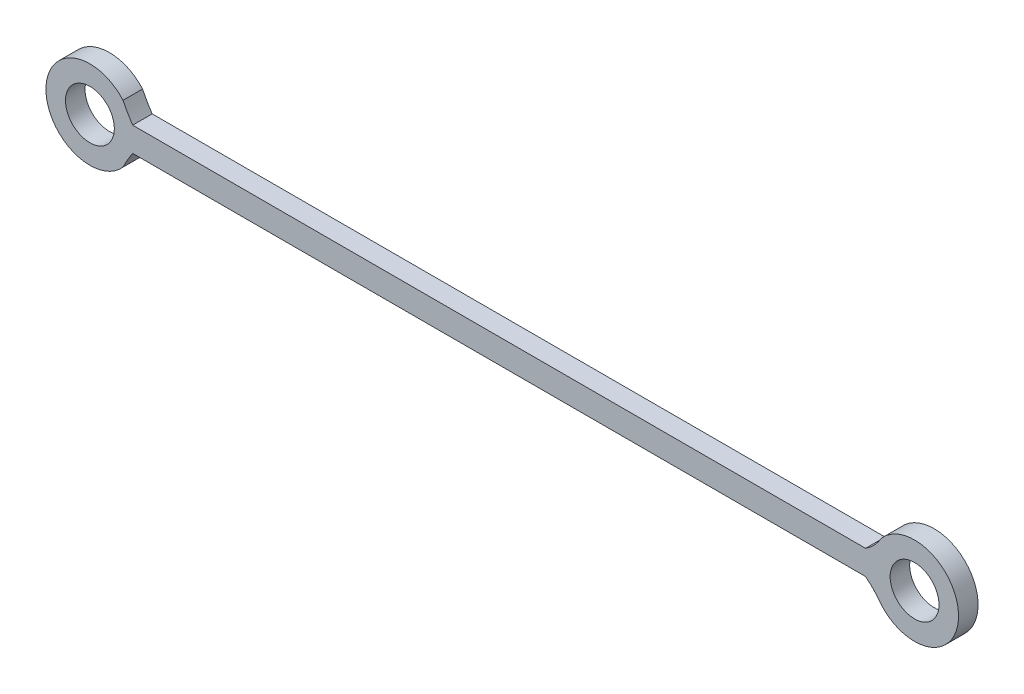
SolidWorks part; units mm, degrees
ref_plane "前视基准面" through (0, 0, 0) normal (0, 0, 1) x (1, 0, 0)
ref_plane "上视基准面" through (0, 0, 0) normal (0, 1, 0) x (1, 0, 0)
ref_plane "右视基准面" through (0, 0, 0) normal (1, 0, 0) x (0, 0, -1)
sketch "草图1" plane through (0, 0, 0) normal (0, 0, 1) x (1, 0, 0)
  line L0 (-67.4973, -2.5) -> (82.4769, -2.5)
  line L1 (82.4769, 2.5) -> (-67.4973, 2.5)
  line L2 (-124.0379, 0) -> (138.7459, 0) construction
  line L3 (-67.4973, 65.4474) -> (-67.4973, -82.036) construction
  line L4 (0, 70.9224) -> (0, -92.6625) construction
  line L5 (82.4769, 70.9224) -> (82.4769, -95.5597) construction
  circle A0 centre (92.5, 0) radius 5
  circle A1 centre (-76.25, 0) radius 5
  arc A2 (85.722, -5.9211) -> (82.4769, -2.5) centre (72.3573, -15.3486) ccw
  arc A3 (85.722, -5.9211) -> (85.722, 5.9211) centre (92.5, 0) ccw
  arc A4 (82.4769, 2.5) -> (85.722, 5.9211) centre (77.0488, 10.8985) ccw
  arc A5 (-69.472, 5.9211) -> (-67.4973, 2.5) centre (-43.5863, 18.5825) ccw
  arc A6 (-69.472, 5.9211) -> (-69.472, -5.9211) centre (-76.25, 0) ccw
  arc A7 (-67.4973, -2.5) -> (-69.472, -5.9211) centre (-43.5863, -18.5825) ccw
  dimension "D2" = 10
  dimension "D3" = 2.5
  dimension "D1" = 67.4973
  dimension "D6" = 10
  dimension "D5" = 9
  dimension "D9" = 10
  dimension "D4" = 2.5
  dimension "D8" = 168.75
extrude "凸台-拉伸1" add sketch "草图1" along normal blind 4
